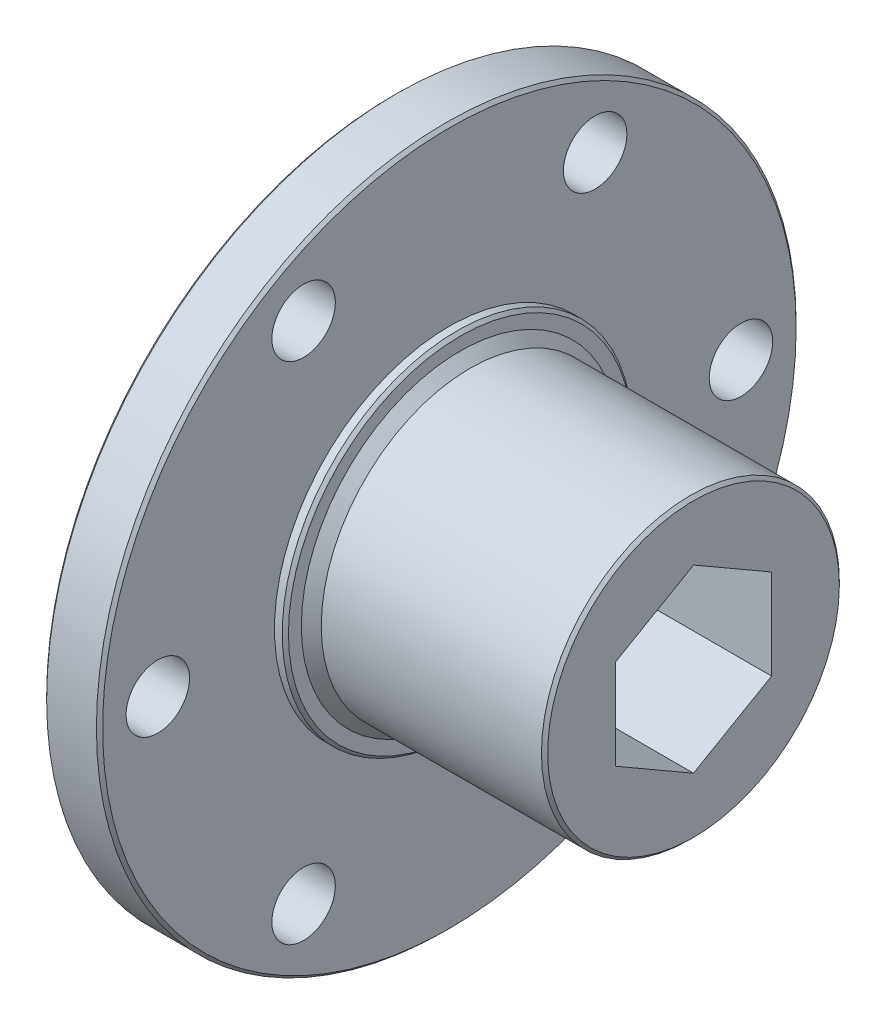
SolidWorks part; units mm, degrees
ref_plane "Front Plane" through (0, 0, 0) normal (0, 0, 1) x (1, 0, 0)
ref_plane "Top Plane" through (0, 0, 0) normal (0, 1, 0) x (1, 0, 0)
ref_plane "Right Plane" through (0, 0, 0) normal (1, 0, 0) x (0, 0, -1)
ref_plane "Plane1" through (0, 0, 0) normal (0, 0, -1) x (-1, 0, 0)
sketch "Sketch1" plane through (0, 0, 0) normal (0, 0, -1) x (-1, 0, 0)
  line L0 (13.9241, 28.575) -> (13.9241, 0)
  line L1 (13.9241, 0) -> (18.4961, 0)
  line L2 (18.4961, 0) -> (18.4961, 28.575)
  line L3 (18.4961, 28.575) -> (13.9241, 28.575)
  line L4 (13.9241, 0) -> (18.4961, 0) construction
revolve "Revolve1" add sketch "Sketch1" angle 360 about L4
sketch "Sketch2" plane through (-13.9241, 0, 0) normal (1, 0, 0) x (0, 0, -1)
  circle A0 centre (0, 0) radius 14.2875
extrude "Boss-Extrude1" add sketch "Sketch2" along normal blind 0.889
sketch "Sketch3" plane through (-13.0351, 0, 0) normal (1, 0, 0) x (0, 0, -1)
  circle A0 centre (0, 0) radius 12.9794
extrude "Boss-Extrude2" add sketch "Sketch3" along normal blind 0.8128 draft 45
sketch "Sketch4" plane through (-12.2223, 0, 0) normal (1, 0, 0) x (0, 0, -1)
  circle A0 centre (0, 0) radius 12.1666
extrude "Boss-Extrude3" add sketch "Sketch4" along normal blind 18.2372
sketch "Sketch5" plane through (-18.4961, 0, 0) normal (-1, 0, 0) x (0, 0, 1)
  circle A0 centre (0, 0) radius 14.2875
extrude "Boss-Extrude4" add sketch "Sketch5" along normal blind 0.889
sketch "Sketch6" plane through (-19.3851, 0, 0) normal (-1, 0, 0) x (0, 0, 1)
  line L0 (0, 7.3617) -> (-6.3754, 3.6808)
  line L1 (-6.3754, 3.6808) -> (-6.3754, -3.6809)
  line L2 (-6.3754, -3.6809) -> (0, -7.3617)
  line L3 (0, -7.3617) -> (6.3754, -3.6809)
  line L4 (6.3754, -3.6809) -> (6.3754, 3.6808)
  line L5 (6.3754, 3.6808) -> (0, 7.3617)
extrude "Cut-Extrude1" cut sketch "Sketch6" against normal through all
hole_wizard "Hole1" positions "Sketch8" profile "Sketch7" legacy
sketch "Sketch8" plane through (-18.4961, 0, 0) normal (-1, 0, 0) x (0, 0, 1)
  point P0 (11.9063, 20.6222)
  point P1 (-23.8125, 0)
  point P2 (11.9062, -20.6222)
  point P3 (-11.9063, -20.6222)
  point P4 (-11.9062, 20.6222)
  point P5 (23.8125, 0)
sketch "Sketch7" plane through (-18.4961, 20.6222, 11.9063) normal (0, 1, 0) x (0, 0, 1)
  line L0 (0, 0) -> (0, 24.511)
  line L1 (0, 24.511) -> (2.5908, 24.511)
  line L2 (2.5908, 24.511) -> (2.5908, 0)
  line L3 (2.5908, 0) -> (0, 0)
  line L4 (0, 110) -> (0, -10) construction
  dimension "Diameter" = 5.1816
  dimension "Depth" = 24.511
chamfer "Chamfer1" distance 0.254 angle 45 5 edges at (-19.3851, 0, 14.2875) (6.0149, 0, -12.1666) (-18.4961, 0, 28.575) (-13.0351, 0, -14.2875) (-13.9241, 0, 28.575)
